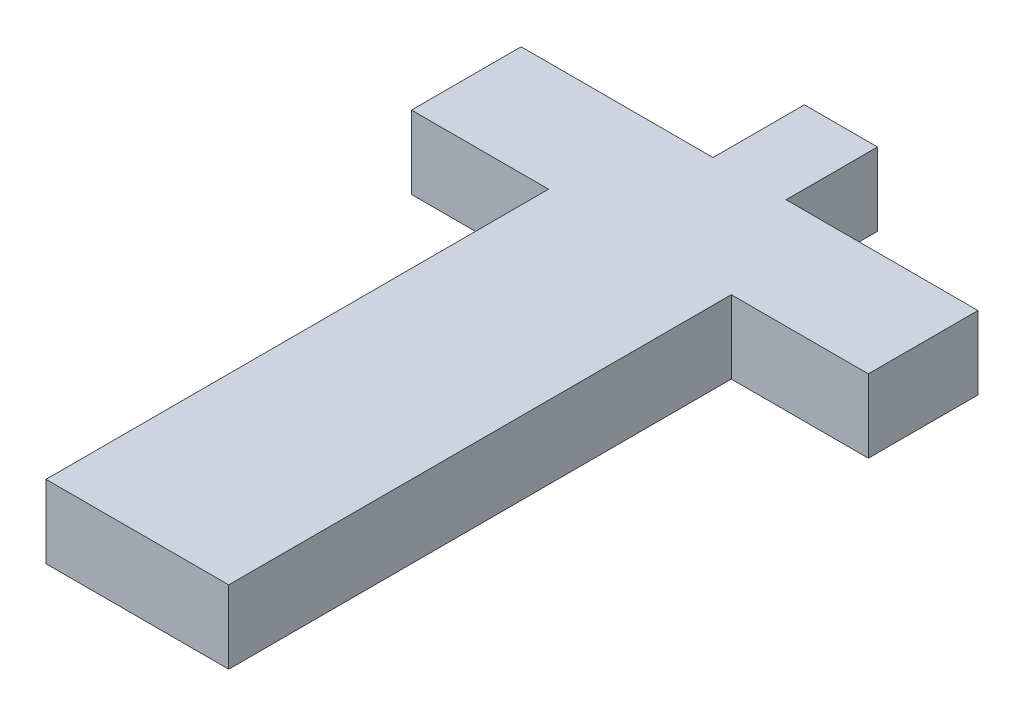
SolidWorks part; units mm, degrees
ref_plane "正面" through (0, 0, 0) normal (0, 0, 1) x (1, 0, 0)
ref_plane "平面" through (0, 0, 0) normal (0, 1, 0) x (1, 0, 0)
ref_plane "右側面" through (0, 0, 0) normal (1, 0, 0) x (0, 0, -1)
sketch "ｽｹｯﾁ1" plane through (0, 0, 0) normal (0, 0, 1) x (1, 0, 0)
  line L1 (-10, 4) -> (10, 4)
  line L2 (-10, 4) -> (-10, -4)
  line L3 (-10, -4) -> (10, -4)
  line L4 (10, 4) -> (10, -4)
  line L5 (-10, 4) -> (10, -4) construction
  line L6 (-10, -4) -> (10, 4) construction
  point P0 (0, 0)
  dimension "D1" = 8
  dimension "D2" = 20
extrude "ﾎﾞｽ - 押し出し1" add sketch "ｽｹｯﾁ1" along normal blind 12
sketch "ｽｹｯﾁ5" plane through (0, 0, 0) normal (0, 0, -1) x (-1, 0, 0)
  line L1 (-4, -4) -> (4, -4)
  line L2 (-4, -4) -> (-4, 4)
  line L3 (-4, 4) -> (4, 4)
  line L4 (4, -4) -> (4, 4)
  line L5 (-4, -4) -> (4, 4) construction
  line L6 (-4, 4) -> (4, -4) construction
  point P0 (0, 0)
  dimension "D1" = 8
  dimension "D2" = 8
extrude "ﾎﾞｽ - 押し出し5" add sketch "ｽｹｯﾁ5" along normal blind 10
sketch "ｽｹｯﾁ8" plane through (0, 0, 12) normal (0, 0, 1) x (1, 0, 0)
  line L1 (10, 4) -> (-10, 4)
  line L2 (10, 4) -> (10, -4)
  line L3 (10, -4) -> (-10, -4)
  line L4 (-10, 4) -> (-10, -4)
extrude "ﾎﾞｽ - 押し出し6" add sketch "ｽｹｯﾁ8" along normal blind 55
sketch "ｽｹｯﾁ9" plane through (10, 0, 0) normal (1, 0, 0) x (0, 0, -1)
  line L1 (-12, 4) -> (0, 4)
  line L2 (-12, 4) -> (-12, -4)
  line L3 (-12, -4) -> (0, -4)
  line L4 (0, 4) -> (0, -4)
extrude "ﾎﾞｽ - 押し出し7" add sketch "ｽｹｯﾁ9" along normal blind 15
sketch "ｽｹｯﾁ10" plane through (-10, 0, 0) normal (-1, 0, 0) x (0, 0, 1)
  line L1 (12, -4) -> (0, -4)
  line L2 (12, -4) -> (12, 4)
  line L3 (12, 4) -> (0, 4)
  line L4 (0, -4) -> (0, 4)
extrude "ﾎﾞｽ - 押し出し8" add sketch "ｽｹｯﾁ10" along normal blind 15
